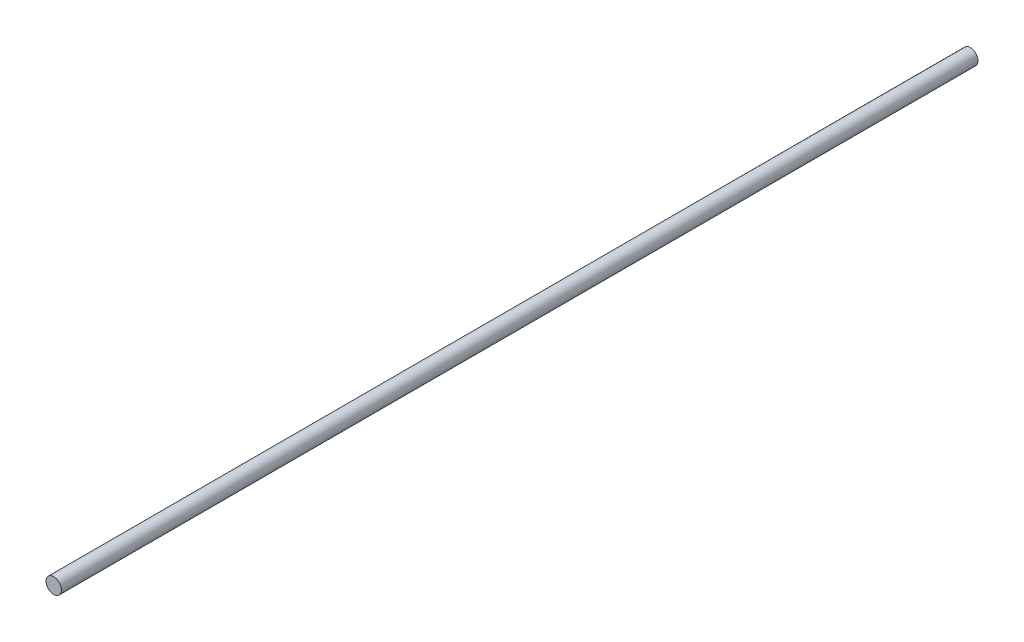
SolidWorks part; units mm, degrees
ref_plane "Plan de face" through (0, 0, 0) normal (0, 0, 1) x (1, 0, 0)
ref_plane "Plan de dessus" through (0, 0, 0) normal (0, 1, 0) x (1, 0, 0)
ref_plane "Plan de droite" through (0, 0, 0) normal (1, 0, 0) x (0, 0, -1)
sketch "Esquisse1" plane through (0, 0, 0) normal (0, 0, 1) x (1, 0, 0)
  circle A0 centre (0, 0) radius 2
  dimension "D1" = 4
extrude "Boss.-Extru.1" add sketch "Esquisse1" along normal blind 238
